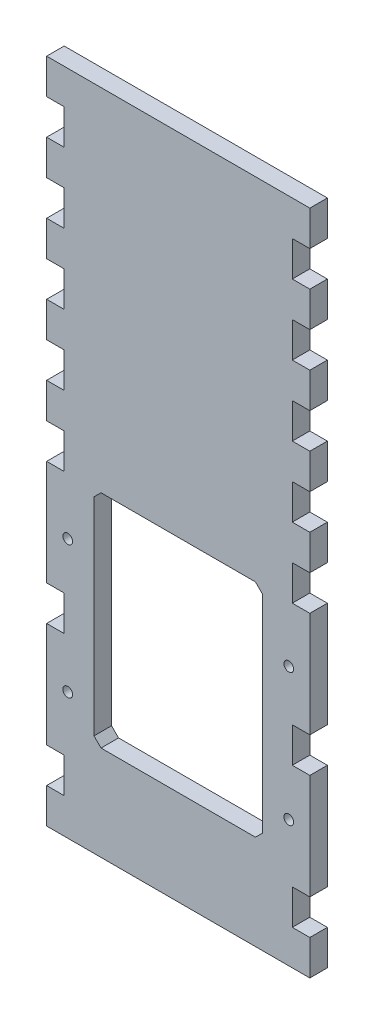
SolidWorks part; units mm, degrees
material "Pine"
ref_plane "Front Plane" through (0, 0, 0) normal (0, 0, 1) x (1, 0, 0)
ref_plane "Top Plane" through (0, 0, 0) normal (0, 1, 0) x (1, 0, 0)
ref_plane "Right Plane" through (0, 0, 0) normal (1, 0, 0) x (0, 0, -1)
sketch "Sketch1" plane through (0, 0, 0) normal (0, 0, 1) x (1, 0, 0)
  line L1 (0, 0) -> (95.25, 0)
  line L2 (0, 0) -> (0, 241.3)
  line L3 (0, 241.3) -> (95.25, 241.3)
  line L4 (95.25, 0) -> (95.25, 241.3)
  dimension "D1" = 95.25
  dimension "D2" = 241.3
extrude "Boss-Extrude1" add sketch "Sketch1" along normal blind 6.35 contours L2 L3 L4 L1
sketch "Sketch2" plane through (0, 0, 6.35) normal (0, 0, 1) x (1, 0, 0)
  line L0 (0, 0) -> (0, 241.3) construction
  line L1 (0, 228.6) -> (6.35, 228.6)
  line L2 (0, 228.6) -> (0, 215.9)
  line L3 (0, 215.9) -> (6.35, 215.9)
  line L4 (6.35, 228.6) -> (6.35, 215.9)
  line L5 (95.25, 0) -> (95.25, 241.3) construction
  line L6 (95.25, 228.6) -> (88.9, 228.6)
  line L7 (95.25, 228.6) -> (95.25, 215.9)
  line L8 (95.25, 215.9) -> (88.9, 215.9)
  line L9 (88.9, 228.6) -> (88.9, 215.9)
  line L10 (0, 241.3) -> (95.25, 241.3) construction
  dimension "D1" = 12.7
  dimension "D2" = 12.7
  dimension "D3" = 6.35
extrude "Cut-Extrude1" cut sketch "Sketch2" against normal through all
pattern_linear "LPattern1" count 9 spacing 25.4 along (0, -1, 0) skipping (5, 0), (7, 0) of "Cut-Extrude1"
sketch "Sketch3" plane through (0, 0, 6.35) normal (0, 0, 1) x (1, 0, 0)
  line L0 (6.35, 69.85) -> (7.625, 69.85) construction
  line L1 (7.625, 93.85) -> (87.625, 93.85) construction
  line L2 (7.625, 93.85) -> (7.625, 45.85) construction
  line L3 (7.625, 45.85) -> (87.625, 45.85) construction
  line L4 (87.625, 93.85) -> (87.625, 45.85) construction
  line L5 (6.35, 63.5) -> (6.35, 76.2) construction
  line L6 (87.625, 69.85) -> (88.9, 69.85) construction
  line L7 (88.9, 76.2) -> (88.9, 63.5) construction
  circle A0 centre (7.625, 93.85) radius 1.75
  circle A1 centre (7.625, 45.85) radius 1.75
  circle A2 centre (87.625, 93.85) radius 1.75
  circle A3 centre (87.625, 45.85) radius 1.75
  dimension "D3" = 3.5
  dimension "D1" = 48
  dimension "D2" = 80
extrude "Cut-Extrude2" cut sketch "Sketch3" against normal through all
sketch "Sketch4" plane through (0, 0, 6.35) normal (0, 0, 1) x (1, 0, 0)
  line L0 (47.625, 39.37) -> (47.625, 0) construction
  line L1 (22.225, 109.22) -> (73.025, 109.22) construction
  line L2 (22.225, 109.22) -> (22.225, 39.37) construction
  line L3 (22.225, 39.37) -> (73.025, 39.37) construction
  line L4 (73.025, 109.22) -> (73.025, 39.37) construction
  line L5 (0, 0) -> (95.25, 0) construction
  line L6 (17.145, 114.3) -> (17.145, 34.29)
  line L7 (17.145, 34.29) -> (78.105, 34.29)
  line L8 (78.105, 114.3) -> (78.105, 34.29)
  line L9 (17.145, 114.3) -> (78.105, 114.3)
  dimension "D1" = 50.8
  dimension "D2" = 69.85
  dimension "D3" = 109.22
  dimension "D4" = 5.08
extrude "Cut-Extrude3" cut sketch "Sketch4" against normal through all
chamfer "Chamfer1" distance 2.54 angle 45 4 edges at (17.145, 34.29, 3.175) (78.105, 34.29, 3.175) (78.105, 114.3, 3.175) (17.145, 114.3, 3.175)
